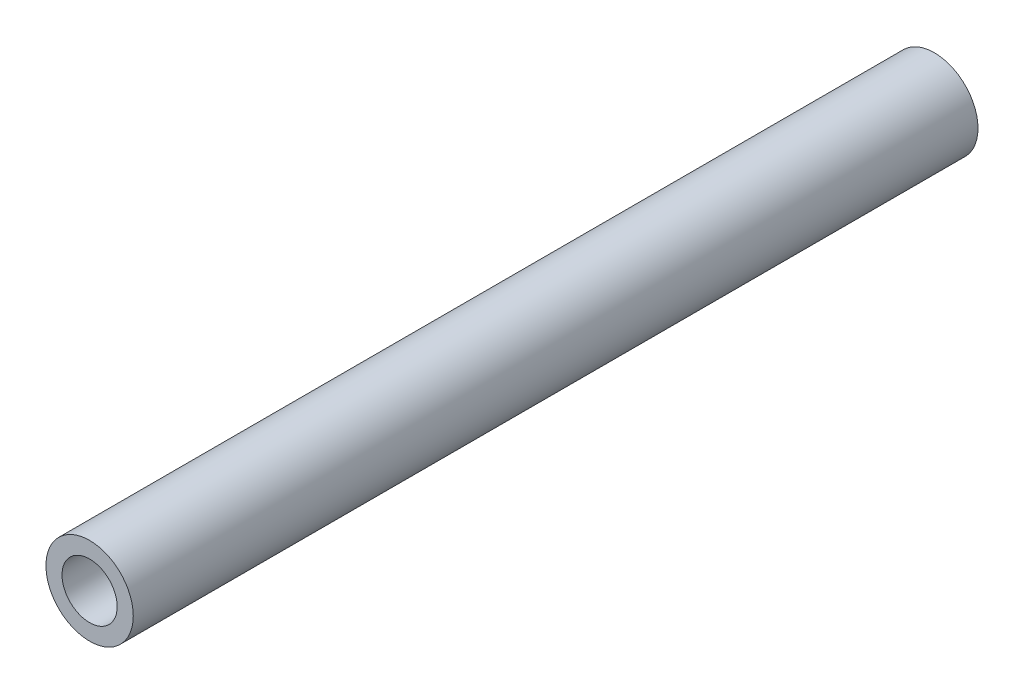
SolidWorks part; units mm, degrees
material "Polyurethane Foam Flexible"
ref_plane "Front Plane" through (0, 0, 0) normal (0, 0, 1) x (1, 0, 0)
ref_plane "Top Plane" through (0, 0, 0) normal (0, 1, 0) x (1, 0, 0)
ref_plane "Right Plane" through (0, 0, 0) normal (1, 0, 0) x (0, 0, -1)
sketch "Sketch1" plane through (0, 0, 0) normal (0, 0, 1) x (1, 0, 0)
  circle A0 centre (0, 0) radius 24.13
  circle A1 centre (0, 0) radius 15.24
  dimension "D1" = 48.26
  dimension "D2" = 30.48
extrude "Boss-Extrude1" add sketch "Sketch1" along normal mid plane 466.725
